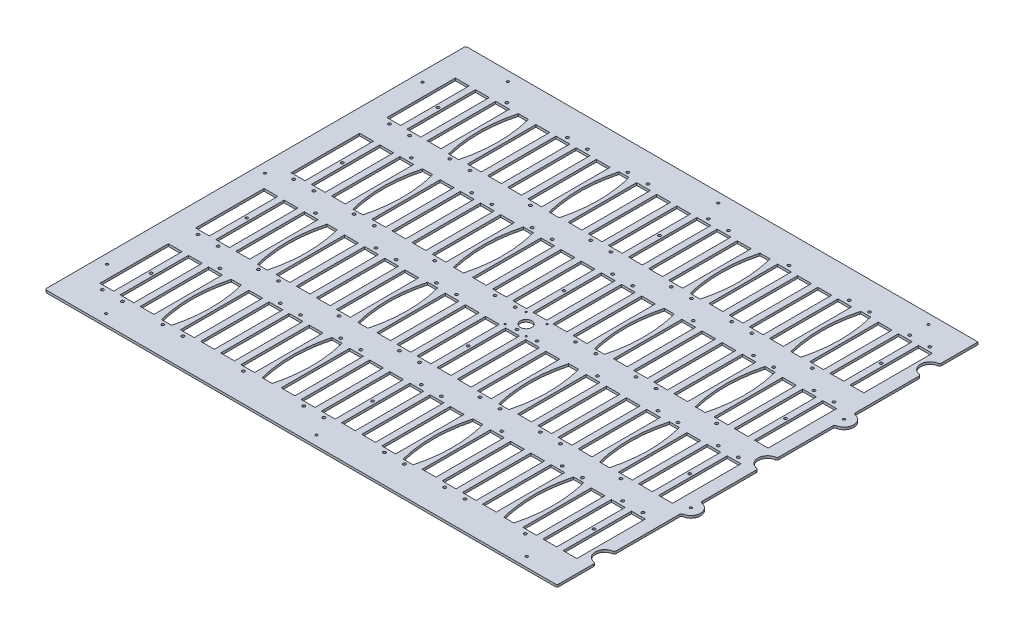
SolidWorks part; units mm, degrees
ref_plane "Front Plane" through (0, 0, 0) normal (0, 0, 1) x (1, 0, 0)
ref_plane "Top Plane" through (0, 0, 0) normal (0, 1, 0) x (1, 0, 0)
ref_plane "Right Plane" through (0, 0, 0) normal (1, 0, 0) x (0, 0, -1)
sketch "Sketch1" plane through (0, 0, 0) normal (0, 1, 0) x (1, 0, 0)
  line L0 (-340.1822, 0) -> (340.1822, 0) construction
  line L1 (-340.1822, -279.5524) -> (340.1822, -279.5524)
  line L2 (-340.1822, -279.5524) -> (-340.1822, 279.5524)
  line L3 (-340.1822, 279.5524) -> (340.1822, 279.5524)
  line L4 (340.1822, -279.5524) -> (340.1822, -228.7524)
  line L5 (-340.1822, -279.5524) -> (340.1822, 279.5524) construction
  line L6 (-340.1822, 279.5524) -> (340.1822, -279.5524) construction
  line L7 (340.1822, -89.0524) -> (340.1822, -12.7)
  line L8 (340.1822, -203.3524) -> (340.1822, -114.4524)
  line L9 (340.1822, 12.7) -> (340.1822, 89.0524)
  line L10 (340.1822, 114.4524) -> (340.1822, 203.3524)
  line L11 (340.1822, 228.7524) -> (340.1822, 279.5524)
  arc A0 (340.1822, 12.7) -> (340.1822, -12.7) centre (340.1822, 0) ccw
  arc A1 (340.1822, -114.4524) -> (340.1822, -89.0524) centre (340.1822, -101.7524) ccw
  arc A2 (340.1822, 89.0524) -> (340.1822, 114.4524) centre (340.1822, 101.7524) ccw
  arc A3 (340.1822, -203.3524) -> (340.1822, -228.7524) centre (340.1822, -216.0524) ccw
  arc A4 (340.1822, 228.7524) -> (340.1822, 203.3524) centre (340.1822, 216.0524) ccw
  point P0 (0, 0)
  dimension "D3" = 63.5
  dimension "D4" = 12.7
  dimension "D5" = 63.5
  dimension "D6" = 177.8
  dimension "D7" = 177.8
  dimension "D1" = 559.1048
  dimension "D2" = 680.3644
extrude "Boss-Extrude1" add sketch "Sketch1" along normal blind 3.175
sketch "Sketch23" plane through (0, 3.175, 0) normal (0, 1, 0) x (1, 0, 0)
  line L1 (322.8848, -236.0422) -> (304.5968, -236.0422)
  line L2 (322.8848, -236.0422) -> (322.8848, -145.1102)
  line L3 (322.8848, -145.1102) -> (304.5968, -145.1102)
  line L4 (304.5968, -236.0422) -> (304.5968, -145.1102)
  line L5 (340.1822, -203.3524) -> (340.1822, -114.4524) construction
  line L6 (-340.1822, -279.5524) -> (340.1822, -279.5524) construction
  dimension "D1" = 90.932
  dimension "D2" = 18.288
  dimension "D3" = 17.2974
  dimension "D4" = 43.5102
extrude "Cut-Extrude7" cut sketch "Sketch23" against normal through all
pattern_linear "LPattern1" count 24 spacing 26.7473 along (-1, 0, 0) skipping (3, 0), (8, 0), (15, 0), (20, 0) of "Cut-Extrude7"
pattern_linear "LPattern2" count 4 spacing 127.0762 along (0, 0, -1) of "LPattern1", "Cut-Extrude7"
sketch "Sketch24" plane through (0, 3.175, 0) normal (0, 1, 0) x (1, 0, 0)
  line L0 (251.1022, -236.0422) -> (215.8955, -145.1102) construction
  line L1 (220.7989, -190.5762) -> (246.1989, -190.5762) construction
  line L2 (240.1029, -144.2212) -> (226.8949, -144.2212)
  line L3 (240.1029, -144.2212) -> (240.1029, -236.9312) construction
  line L4 (240.1029, -236.9312) -> (226.8949, -236.9312)
  line L5 (226.8949, -144.2212) -> (226.8949, -236.9312) construction
  line L6 (240.1029, -144.2212) -> (226.8949, -236.9312) construction
  line L7 (240.1029, -236.9312) -> (226.8949, -144.2212) construction
  line L8 (106.3663, -236.9312) -> (93.1583, -236.9312)
  line L9 (106.3663, -144.2212) -> (93.1583, -144.2212)
  spline S0 degree 2 poles (226.8949, -236.9312) (214.7029, -190.5762) (226.8949, -144.2212) knots 0 0 0 1 1 1
  spline S1 degree 2 poles (240.1029, -236.9312) (252.2949, -190.5762) (240.1029, -144.2212) knots 0 0 0 1 1 1
  spline S2 degree 2 poles (93.1583, -236.9312) (80.9663, -190.5762) (93.1583, -144.2212) knots 0 0 0 1 1 1
  spline S3 degree 2 poles (106.3663, -236.9312) (118.5583, -190.5762) (106.3663, -144.2212) knots 0 0 0 1 1 1
  point P4 (233.4989, -190.5762)
  point P12 (233.4989, -190.5762)
  dimension "D1" = 13.208
  dimension "D2" = 92.71
  dimension "D3" = 25.4
  dimension "D4" = 2
extrude "Cut-Extrude8" cut sketch "Sketch24" against normal through all
pattern_linear "LPattern3" count 2 spacing 320.9678 along (1, 0, 0) count 4 spacing 127.0762 along (0, 0, -1) of "Cut-Extrude8"
hole_wizard "#25 (0.1495) Diameter Hole1" positions "Sketch18" profile "Sketch19" hole size "#25" standard "ANSI Inch" end condition through all
sketch "Sketch18" plane through (0, 3.175, 0) normal (0, 1, 0) x (1, 0, 0)
  line L64 (313.7408, -145.1102) -> (313.7408, -139.2682) construction
  line L65 (322.8848, -145.1102) -> (304.5968, -145.1102) construction
  point P771 (313.7408, -139.2682)
  dimension "D1" = 5.842
sketch "Sketch19" plane through (313.7408, 3.175, 139.2682) normal (1, 0, 0) x (0, 0, 1)
  line L0 (0, 0) -> (0, 3.175)
  line L1 (0, 3.175) -> (1.8986, 3.175)
  line L2 (1.8986, 3.175) -> (1.8986, 0)
  line L5 (1.8986, 0) -> (0, 0)
  line L11 (0, -6.35) -> (0, 107.95) construction
  dimension "Thru Hole Dia." = 3.7973
  dimension "Thru Hole Depth" = 3.175
hole_wizard "#25 (0.1495) Diameter Hole2" positions "Sketch25" profile "Sketch26" hole size "#25" standard "ANSI Inch" end condition up to next
sketch "Sketch25" plane through (0, 3.175, 0) normal (0, 1, 0) x (1, 0, 0)
  line L0 (260.2462, -241.8842) -> (260.2462, -236.0422) construction
  line L1 (251.1022, -236.0422) -> (269.3902, -236.0422) construction
  point P0 (260.2462, -241.8842)
  dimension "D1" = 5.842
sketch "Sketch26" plane through (260.2462, 3.175, 241.8842) normal (1, 0, 0) x (0, 0, 1)
  line L0 (0, 0) -> (0, 3.176)
  line L1 (0, 3.176) -> (1.8986, 3.176)
  line L2 (1.8986, 3.176) -> (1.8986, 0)
  line L5 (1.8986, 0) -> (0, 0)
  line L11 (0, -6.35) -> (0, 107.95) construction
  dimension "Thru Hole Dia." = 3.7973
  dimension "Thru Hole Depth" = 3.176
pattern_linear "LPattern4" count 24 spacing 26.7473 along (-1, 0, 0) skipping (2, 0), (5, 0), (6, 0), (8, 0), (9, 0), (12, 0), (13, 0), (16, 0), (19, 0), (20, 0), (22, 0), (23, 0) of "#25 (0.1495) Diameter Hole1"
pattern_linear "LPattern6" count 22 spacing 26.7473 along (-1, 0, 0) skipping (1, 0), (2, 0), (5, 0), (8, 0), (9, 0), (12, 0), (13, 0), (15, 0), (16, 0), (19, 0) of "#25 (0.1495) Diameter Hole2"
pattern_linear "LPattern5" count 4 spacing 127.0762 along (0, 0, -1) of "LPattern4", "LPattern6", "#25 (0.1495) Diameter Hole1", "#25 (0.1495) Diameter Hole2"
fillet "Fillet1" radius 2.54 13 edges at (-340.1822, 1.5875, -279.5524) (-340.1822, 1.5875, 279.5524) (340.1822, 1.5875, 279.5524) (340.1822, 1.5875, 203.3524) (340.1822, 1.5875, 228.7524) (340.1822, 1.5875, -228.7524) (340.1822, 1.5875, -203.3524) (340.1822, 1.5875, -114.4524) (340.1822, 1.5875, -89.0524) (340.1822, 1.5875, -12.7) (340.1822, 1.5875, 12.7) (340.1822, 1.5875, 89.0524) (340.1822, 1.5875, 114.4524)
hole_wizard "#6 Clearance Hole2" positions "Sketch27" profile "Sketch28" hole size "#6" standard "ANSI Inch"
sketch "Sketch27" plane through (0, 3.175, 0) normal (0, 1, 0) x (1, 0, 0)
  line L0 (304.5968, -236.0422) -> (296.1375, -145.1102) construction
  line L1 (296.1375, -236.0422) -> (296.1375, -145.1102) construction
  line L2 (296.1375, -145.1102) -> (277.8495, -145.1102) construction
  point P10 (300.3671, -190.5762)
  point P20 (6.1467, -190.5762)
  point P21 (-288.0737, -190.5762)
  point P22 (6.1467, -63.5)
  point P23 (-288.0737, -63.5)
  point P24 (6.1467, 63.5762)
  point P25 (-288.0737, 63.5762)
  point P26 (6.1467, 190.6524)
  point P27 (-288.0737, 190.6524)
  point P28 (300.3671, -63.5)
  point P29 (300.3671, 63.5762)
  point P30 (300.3671, 190.6524)
  dimension "D1" = 4
sketch "Sketch28" plane through (300.3671, 3.175, -190.6524) normal (1, 0, 0) x (0, 0, 1)
  line L0 (0, 0) -> (0, 3.175)
  line L1 (0, 3.175) -> (1.8288, 3.175)
  line L2 (1.8288, 3.175) -> (1.8288, 0)
  line L5 (1.8288, 0) -> (0, 0)
  line L11 (0, -6.35) -> (0, 107.95) construction
  dimension "Thru Hole Dia." = 3.6576
  dimension "Thru Hole Depth" = 3.175
hole_wizard "#2 Clearance Hole2" positions "Sketch29" profile "Sketch30" hole size "#2" standard "ANSI Inch"
sketch "Sketch29" plane through (0, 3.175, 0) normal (0, 1, 0) x (1, 0, 0)
  line L23 (5.5504, 14.0081) -> (33.4904, 14.0081) construction
  line L24 (5.5504, 14.0081) -> (5.5504, -13.9319) construction
  line L25 (5.5504, -13.9319) -> (33.4904, -13.9319) construction
  line L26 (33.4904, 14.0081) -> (33.4904, -13.9319) construction
  line L27 (5.5504, 14.0081) -> (33.4904, -13.9319) construction
  line L28 (5.5504, -13.9319) -> (33.4904, 14.0081) construction
  line L30 (28.6644, -18.034) -> (10.3764, 18.1102) construction
  point P135 (33.4904, -13.9319)
  point P146 (5.5504, 14.0081)
  point P147 (5.5504, -13.9319)
  point P148 (33.4904, 14.0081)
  point P175 (0, 0)
  dimension "D1" = 27.94
sketch "Sketch30" plane through (33.4904, 3.175, 13.9319) normal (1, 0, 0) x (0, 0, 1)
  line L0 (0, 0) -> (0, 3.175)
  line L1 (0, 3.175) -> (1.1303, 3.175)
  line L2 (1.1303, 3.175) -> (1.1303, 0)
  line L5 (1.1303, 0) -> (0, 0)
  line L11 (0, -6.35) -> (0, 107.95) construction
  dimension "Thru Hole Dia." = 2.2606
  dimension "Thru Hole Depth" = 3.175
sketch "Sketch20" plane through (0, 3.175, 0) normal (0, 1, 0) x (1, 0, 0)
  line L0 (33.4904, -13.9319) -> (5.5504, 14.0081) construction
  circle A0 centre (19.5204, 0.0381) radius 7.62
  dimension "D1" = 15.24
extrude "Cut-Extrude6" cut sketch "Sketch20" against normal through all
hole_wizard "1/8 (0.125) Diameter Hole1" positions "Sketch21" profile "Sketch22" hole size "1/8" standard "ANSI Inch"
sketch "Sketch21" plane through (0, 3.175, 0) normal (0, 1, 0) x (1, 0, 0)
  point P0 (287.274, -266.8524)
  point P12 (287.274, 266.8524)
  point P15 (7.874, 266.8524)
  point P18 (-271.526, 266.8524)
  point P21 (-327.5584, 209.55)
  point P24 (-327.5584, 0)
  point P27 (-327.5584, -209.55)
  point P30 (-271.526, -266.8524)
  point P33 (7.874, -266.8524)
  point P56 (340.1822, 101.7524)
  point P59 (340.1822, -101.7524)
sketch "Sketch22" plane through (287.274, 3.175, 266.8524) normal (1, 0, 0) x (0, 0, 1)
  line L0 (0, 0) -> (0, 3.175)
  line L1 (0, 3.175) -> (1.5875, 3.175)
  line L2 (1.5875, 3.175) -> (1.5875, 0)
  line L5 (1.5875, 0) -> (0, 0)
  line L11 (0, -6.35) -> (0, 107.95) construction
  dimension "Thru Hole Dia." = 3.175
  dimension "Thru Hole Depth" = 3.175
